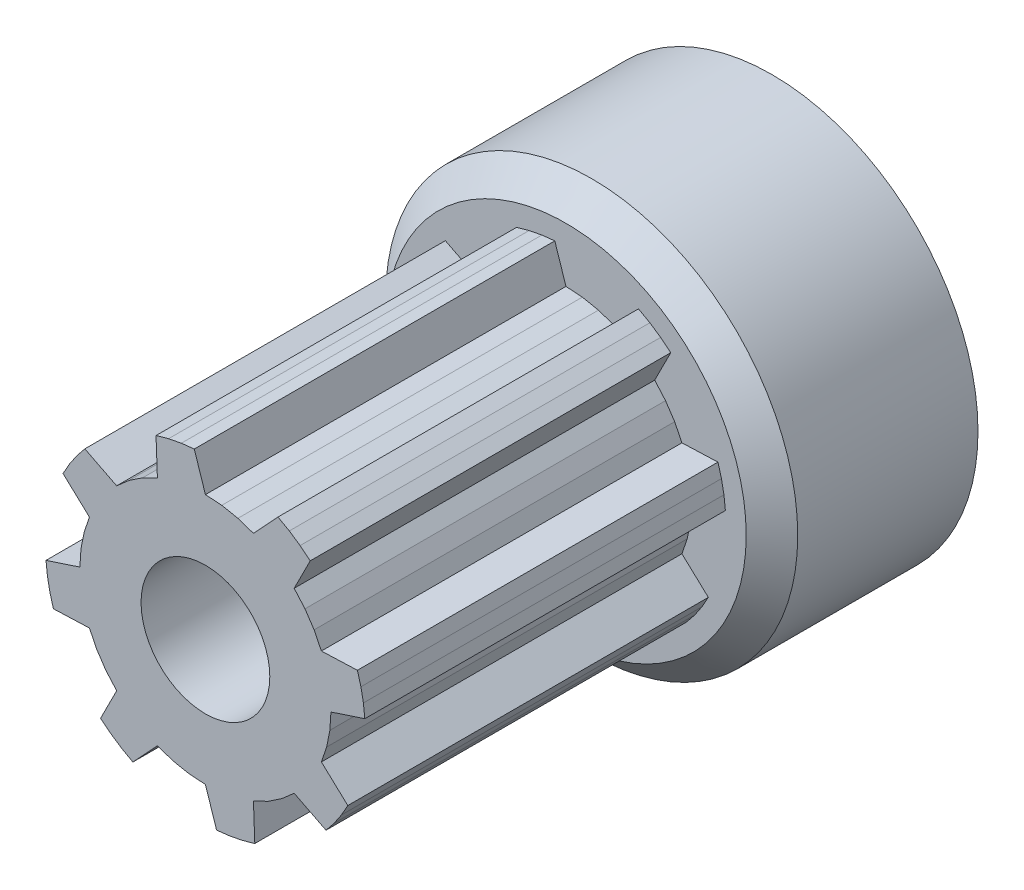
SolidWorks part; units mm, degrees
material "Green ABS"
ref_plane "Front Plane" through (0, 0, 0) normal (0, 0, 1) x (1, 0, 0)
ref_plane "Top Plane" through (0, 0, 0) normal (0, 1, 0) x (1, 0, 0)
ref_plane "Right Plane" through (0, 0, 0) normal (1, 0, 0) x (0, 0, -1)
sketch "Sketch2" plane through (0, 0, 0) normal (0, 0, 1) x (1, 0, 0)
  line L2 (4.8737, 0) -> (4.832, -0.6361)
  line L3 (4.832, -0.6361) -> (4.7076, -1.2614)
  line L7 (4.7076, -1.2614) -> (4.5027, -1.8651)
  line L18 (5.529, -2.8172) -> (5.2815, -3.2577)
  line L20 (4.5027, -1.8651) -> (5.529, -2.8172)
  line L25 (5.2815, -3.2577) -> (4.999, -3.6766)
  line L27 (4.6833, -4.0711) -> (3.4462, -3.4462)
  line L29 (4.999, -3.6766) -> (4.6833, -4.0711)
  line L30 (3.4462, -3.4462) -> (2.9669, -3.8666)
  line L34 (2.9669, -3.8666) -> (2.4369, -4.2208)
  line L37 (2.4369, -4.2208) -> (1.8651, -4.5027)
  line L43 (0, -4.8737) -> (-0.6361, -4.832)
  line L46 (-0.6361, -4.832) -> (-1.2614, -4.7076)
  line L49 (-1.2614, -4.7076) -> (-1.8651, -4.5027)
  line L56 (-3.4462, -3.4462) -> (-3.8666, -2.9669)
  line L57 (-3.8666, -2.9669) -> (-4.2208, -2.4369)
  line L61 (-4.2208, -2.4369) -> (-4.5027, -1.8651)
  line L68 (-4.8737, 0) -> (-4.832, 0.6361)
  line L69 (-4.832, 0.6361) -> (-4.7076, 1.2614)
  line L73 (-4.7076, 1.2614) -> (-4.5027, 1.8651)
  line L84 (1.9176, -5.9017) -> (1.4311, -6.0381)
  line L86 (1.8651, -4.5027) -> (1.9176, -5.9017)
  line L91 (1.4311, -6.0381) -> (0.9351, -6.1345)
  line L93 (0.4329, -6.1903) -> (0, -4.8737)
  line L95 (0.9351, -6.1345) -> (0.4329, -6.1903)
  line L96 (-2.8172, -5.529) -> (-3.2577, -5.2815)
  line L98 (-1.8651, -4.5027) -> (-2.8172, -5.529)
  line L100 (-3.2577, -5.2815) -> (-3.6766, -4.999)
  line L103 (-3.6766, -4.999) -> (-4.0711, -4.6833)
  line L104 (-4.0711, -4.6833) -> (-3.4462, -3.4462)
  line L108 (-5.9017, -1.9176) -> (-6.0381, -1.4311)
  line L110 (-4.5027, -1.8651) -> (-5.9017, -1.9176)
  line L115 (-6.0381, -1.4311) -> (-6.1345, -0.9351)
  line L117 (-6.1903, -0.4329) -> (-4.8737, 0)
  line L119 (-6.1345, -0.9351) -> (-6.1903, -0.4329)
  line L120 (-5.529, 2.8172) -> (-5.2815, 3.2577)
  line L122 (-4.5027, 1.8651) -> (-5.529, 2.8172)
  line L127 (-5.2815, 3.2577) -> (-4.999, 3.6766)
  line L129 (-4.6833, 4.0711) -> (-3.4462, 3.4462)
  line L131 (-4.999, 3.6766) -> (-4.6833, 4.0711)
  line L132 (-3.4462, 3.4462) -> (-2.9669, 3.8666)
  line L136 (-2.9669, 3.8666) -> (-2.4369, 4.2208)
  line L139 (-2.4369, 4.2208) -> (-1.8651, 4.5027)
  line L145 (0, 4.8737) -> (0.6361, 4.832)
  line L148 (0.6361, 4.832) -> (1.2614, 4.7076)
  line L151 (1.2614, 4.7076) -> (1.8651, 4.5027)
  line L158 (3.4462, 3.4462) -> (3.8666, 2.9669)
  line L159 (3.8666, 2.9669) -> (4.2208, 2.4369)
  line L163 (4.2208, 2.4369) -> (4.5027, 1.8651)
  line L171 (-1.9176, 5.9017) -> (-1.4311, 6.0381)
  line L173 (-1.8651, 4.5027) -> (-1.9176, 5.9017)
  line L178 (-1.4311, 6.0381) -> (-0.9351, 6.1345)
  line L180 (-0.4329, 6.1903) -> (0, 4.8737)
  line L182 (-0.9351, 6.1345) -> (-0.4329, 6.1903)
  line L183 (2.8172, 5.529) -> (3.2577, 5.2815)
  line L185 (1.8651, 4.5027) -> (2.8172, 5.529)
  line L187 (3.2577, 5.2815) -> (3.6766, 4.999)
  line L190 (3.6766, 4.999) -> (4.0711, 4.6833)
  line L191 (4.0711, 4.6833) -> (3.4462, 3.4462)
  line L195 (5.9017, 1.9176) -> (6.0381, 1.4311)
  line L197 (4.5027, 1.8651) -> (5.9017, 1.9176)
  line L199 (6.0381, 1.4311) -> (6.1345, 0.9351)
  line L202 (6.1345, 0.9351) -> (6.1903, 0.4329)
  line L203 (6.1903, 0.4329) -> (4.8737, 0)
  circle A0 centre (0, 0) radius 2.5
extrude "Boss-Extrude1" add sketch "Sketch2" along normal blind 14
sketch "Sketch3" plane through (0, 0, 0) normal (0, 0, -1) x (-1, 0, 0)
  circle A0 centre (0, 0) radius 8
extrude "Boss-Extrude2" add sketch "Sketch3" along normal blind 8
sketch "Sketch4" plane through (0, 0, -8) normal (0, 0, -1) x (-1, 0, 0)
  circle A0 centre (0, 0) radius 2.5
extrude "Cut-Extrude1" cut sketch "Sketch4" against normal through all
sketch "Sketch5" plane through (0, 0, 0) normal (0, 1, 0) x (1, 0, 0)
  line L0 (0, 0) -> (0, -15.7839) construction
  line L1 (2.5, -14) -> (7, -14)
  line L2 (7, -14) -> (7, -13.2)
  line L3 (7, -13.2) -> (2.5, -11)
  line L5 (2.5, -11) -> (2.5, -14)
  dimension "D1" = 7
  dimension "D2" = 0.8
  dimension "D3" = 3
  dimension "D4" = 2.5
chamfer "Chamfer1" distance 1 angle 45 1 edges at (-8, 0, 0)
